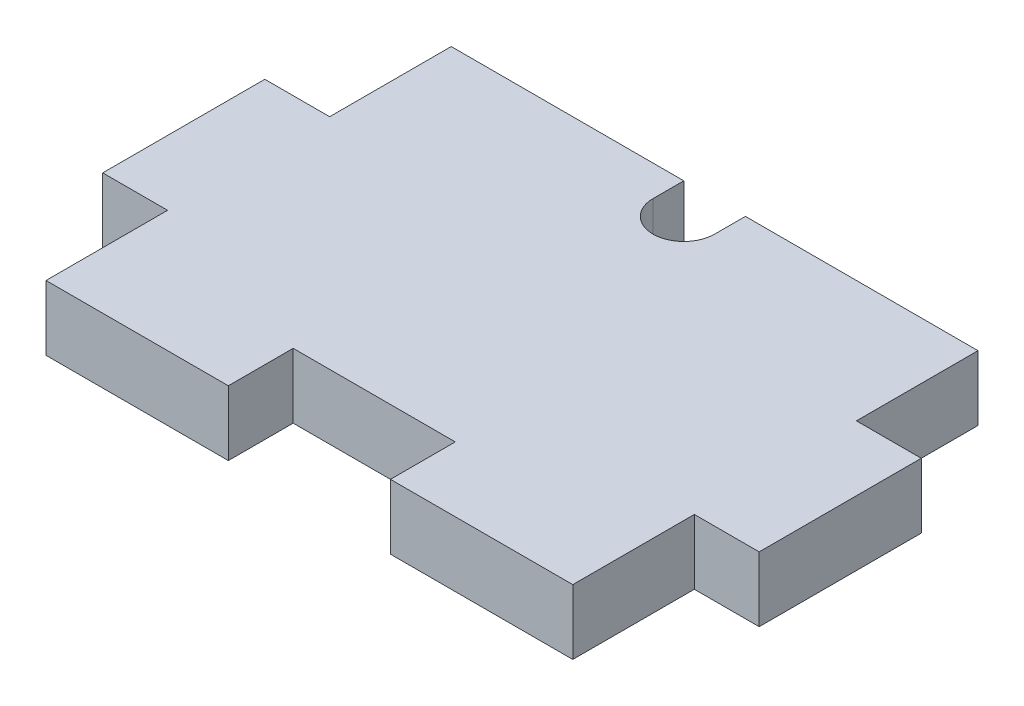
SolidWorks part; units mm, degrees
material "Maple"
ref_plane "Front Plane" through (0, 0, 0) normal (0, 0, 1) x (1, 0, 0)
ref_plane "Top Plane" through (0, 0, 0) normal (0, 1, 0) x (1, 0, 0)
ref_plane "Right Plane" through (0, 0, 0) normal (1, 0, 0) x (0, 0, -1)
sketch "Sketch1" plane through (0, 0, 0) normal (0, 1, 0) x (1, 0, 0)
  line L1 (0, 0) -> (32.5, 0)
  line L2 (0, 0) -> (0, -25)
  line L3 (0, -25) -> (32.5, -25)
  line L4 (32.5, 0) -> (32.5, -25)
  dimension "D1" = 32.5
  dimension "D2" = 25
extrude "Boss-Extrude1" add sketch "Sketch1" along normal blind 4
sketch "Sketch2" plane through (0, 4, 0) normal (0, 1, 0) x (1, 0, 0)
  line L0 (16.25, 0) -> (16.25, -25) construction
  line L1 (32.5, 0) -> (0, 0) construction
  line L2 (0, -25) -> (32.5, -25) construction
  line L4 (14.35, -1.9) -> (18.15, -1.9)
  line L5 (14.35, -1.9) -> (14.35, 0)
  line L6 (14.35, 0) -> (18.15, 0)
  line L7 (18.15, -1.9) -> (18.15, 0)
  circle A0 centre (16.25, -1.9) radius 1.9
  line M4 (32.5, 0) -> (0, 0)
  dimension "D1" = 3.8
extrude "Cut-Extrude5" cut sketch "Sketch2" against normal through all contours L0 L4 A0 | L0 A0 L4 | A0 L6 L5 | A0 L7 M4 | A0 L0 L4 | L4 L0 A0
sketch "Sketch3" plane through (0, 4, 0) normal (0, 1, 0) x (1, 0, 0)
  line L0 (0, -12.5) -> (32.5, -12.5) construction
  line L1 (0, 0) -> (0, -25) construction
  line L2 (32.5, -25) -> (32.5, 0) construction
  line L4 (-4, -7.5) -> (0, -7.5)
  line L5 (-4, -7.5) -> (-4, -17.5)
  line L6 (-4, -17.5) -> (0, -17.5)
  line L7 (0, -7.5) -> (0, -17.5)
  line L8 (-4, -7.5) -> (0, -17.5) construction
  line L9 (-4, -17.5) -> (0, -7.5) construction
  line L10 (32.5, -7.5) -> (36.5, -7.5)
  line L11 (32.5, -7.5) -> (32.5, -17.5)
  line L12 (32.5, -17.5) -> (36.5, -17.5)
  line L13 (36.5, -7.5) -> (36.5, -17.5)
  line L14 (32.5, -7.5) -> (36.5, -17.5) construction
  line L15 (32.5, -17.5) -> (36.5, -7.5) construction
  point P6 (-2, -12.5)
  point P11 (34.5, -12.5)
  dimension "D1" = 4
  dimension "D2" = 10
  dimension "D3" = 10
  dimension "D4" = 4
extrude "Boss-Extrude2" add sketch "Sketch3" against normal through all
sketch "Sketch4" plane through (0, 4, 0) normal (0, 1, 0) x (1, 0, 0)
  line L0 (0, -25) -> (32.5, -25) construction
  line L1 (11.25, -21) -> (21.25, -21)
  line L2 (11.25, -21) -> (11.25, -25)
  line L3 (11.25, -25) -> (21.25, -25)
  line L4 (21.25, -21) -> (21.25, -25)
  point P4 (21.25, -25)
  point P7 (11.8465, -21.7163)
  point P8 (11.25, -21)
extrude "Cut-Extrude6" cut sketch "Sketch4" against normal through all
equation "\"D3@Sketch3\"=\"D2@Sketch3\""
equation "\"D4@Sketch3\"=\"D1@Sketch3\""
